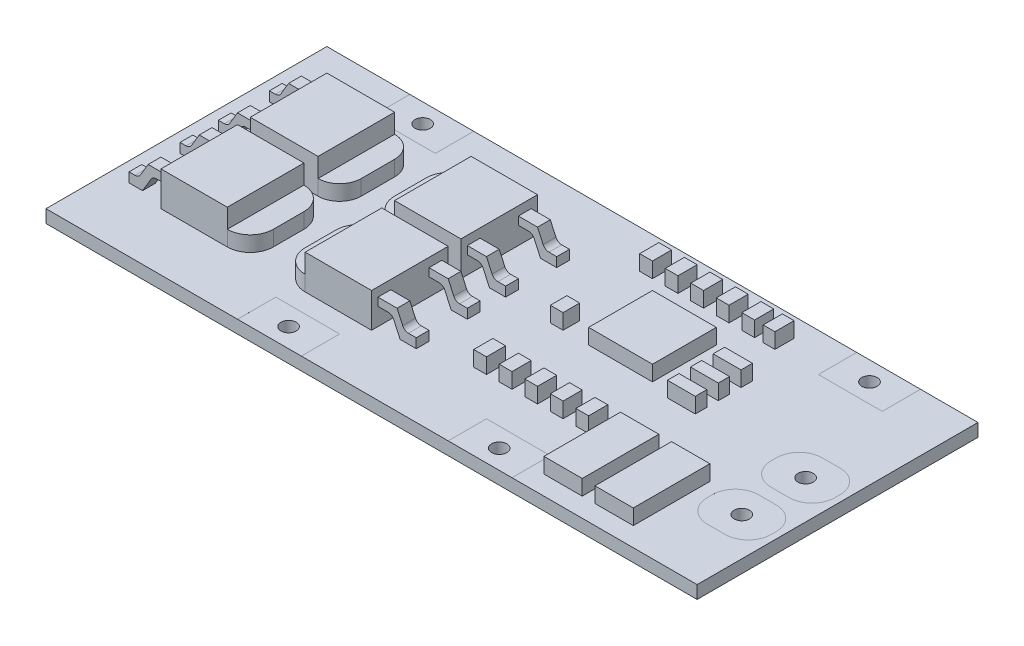
SolidWorks part; units mm, degrees
ref_plane "Front Plane" through (0, 0, 0) normal (0, 0, 1) x (1, 0, 0)
ref_plane "Top Plane" through (0, 0, 0) normal (0, 1, 0) x (1, 0, 0)
ref_plane "Right Plane" through (0, 0, 0) normal (1, 0, 0) x (0, 0, -1)
sketch "Sketch1" plane through (0, 0, 0) normal (0, 1, 0) x (1, 0, 0)
  line L1 (-25.5, 11) -> (25.5, 11)
  line L2 (-25.5, 11) -> (-25.5, -11)
  line L3 (-25.5, -11) -> (25.5, -11)
  line L4 (25.5, 11) -> (25.5, -11)
  circle A0 centre (22.5, 0.5) radius 0.6
  circle A1 centre (22.5, -4.5) radius 0.6
  circle A2 centre (18.5, 9.5) radius 0.6
  circle A3 centre (-16.5, 9.5) radius 0.6
  circle A4 centre (8.5, -9.5) radius 0.6
  circle A5 centre (-8, -9.5) radius 0.6
  point P4 (0, 11)
  point P6 (-25.5, 0)
  point P11 (25.5, 0)
  dimension "D6" = 1.2
  dimension "D7" = 1.2
  dimension "D10" = 1.2
  dimension "D13" = 1.2
  dimension "D16" = 1.2
  dimension "D19" = 1.2
  dimension "D1" = 22
  dimension "D2" = 51
  dimension "D3" = 0
  dimension "D4" = 0
  dimension "D5" = 5
  dimension "D8" = 11.5
  dimension "D9" = 3
  dimension "D11" = 7
  dimension "D12" = 1.5
  dimension "D14" = 35
  dimension "D15" = 1.5
  dimension "D17" = 17
  dimension "D18" = 1.5
  dimension "D20" = 16.5
  dimension "D21" = 1.5
  dimension "D22" = 3
extrude "Boss-Extrude1" add sketch "Sketch1" along normal blind 1 and the other way blind 0.01
sketch "Sketch2" plane through (0, 1, 0) normal (0, 1, 0) x (1, 0, 0)
  line L0 (25.5, 11) -> (-25.5, 11) construction
  line L1 (-19, 11) -> (-14, 11)
  line L2 (-19, 11) -> (-19, 8)
  line L3 (-19, 8) -> (-14, 8)
  line L4 (-14, 11) -> (-14, 8)
  line L5 (16, 11) -> (21, 11)
  line L6 (16, 11) -> (16, 8)
  line L7 (16, 8) -> (21, 8)
  line L8 (21, 11) -> (21, 8)
  line L9 (-25.5, -11) -> (25.5, -11) construction
  line L10 (-10.5, -8) -> (-5.5, -8)
  line L11 (-10.5, -8) -> (-10.5, -11)
  line L12 (-10.5, -11) -> (-5.5, -11)
  line L13 (-5.5, -8) -> (-5.5, -11)
  line L15 (6, -8) -> (11, -8)
  line L16 (6, -8) -> (6, -11)
  line L17 (6, -11) -> (11, -11)
  line L18 (11, -8) -> (11, -11)
  line L19 (21.8, 2.5) -> (23.2, 2.5)
  line L20 (20, 0.7) -> (20, 0.3)
  line L21 (21.8, -1.5) -> (23.2, -1.5)
  line L22 (25, 0.7) -> (25, 0.3)
  line L23 (21.8, -2.5) -> (23.2, -2.5)
  line L24 (20, -4.3) -> (20, -4.7)
  line L25 (21.8, -6.5) -> (23.2, -6.5)
  line L26 (25, -4.3) -> (25, -4.7)
  circle A0 centre (-16.5, 9.5) radius 0.6 construction
  circle A1 centre (18.5, 9.5) radius 0.6 construction
  circle A2 centre (-8, -9.5) radius 0.6 construction
  circle A3 centre (8.5, -9.5) radius 0.6 construction
  circle A4 centre (22.5, -4.5) radius 0.6 construction
  circle A5 centre (22.5, 0.5) radius 0.6 construction
  arc A6 (20, 0.3) -> (21.8, -1.5) centre (21.8, 0.3) ccw
  arc A7 (23.2, -1.5) -> (25, 0.3) centre (23.2, 0.3) ccw
  arc A8 (25, 0.7) -> (23.2, 2.5) centre (23.2, 0.7) ccw
  arc A9 (21.8, 2.5) -> (20, 0.7) centre (21.8, 0.7) ccw
  arc A10 (21.8, -2.5) -> (20, -4.3) centre (21.8, -4.3) ccw
  arc A11 (25, -4.3) -> (23.2, -2.5) centre (23.2, -4.3) ccw
  arc A12 (23.2, -6.5) -> (25, -4.7) centre (23.2, -4.7) ccw
  arc A13 (20, -4.7) -> (21.8, -6.5) centre (21.8, -4.7) ccw
  point P20 (-14, 9.5)
  point P41 (22.5, 2.5)
  dimension "D22" = 1.8
  dimension "D23" = 1.8
  dimension "D24" = 1.8
  dimension "D25" = 1.8
  dimension "D26" = 1.8
  dimension "D1" = 3
  dimension "D2" = 0
  dimension "D3" = 2.5
  dimension "D4" = 2.5
  dimension "D5" = 2.5
  dimension "D6" = 2.5
  dimension "D7" = 3
  dimension "D8" = 3
  dimension "D9" = 2.5
  dimension "D10" = 2.5
  dimension "D11" = 3
  dimension "D12" = 2.5
  dimension "D13" = 2.5
  dimension "D14" = 2.5
  dimension "D15" = 2.5
  dimension "D16" = 2
  dimension "D17" = 2
  dimension "D18" = 2
  dimension "D19" = 2
  dimension "D20" = 2.5
  dimension "D21" = 2.5
extrude "Cut-Extrude1" cut sketch "Sketch2" against normal blind 0.0001
sketch "Sketch3" plane through (0, -0.01, 0) normal (0, -1, 0) x (1, 0, 0)
  line L0 (25.5, -11) -> (-25.5, -11) construction
  line L1 (21, -11) -> (16, -11)
  line L2 (21, -11) -> (21, -8)
  line L3 (21, -8) -> (16, -8)
  line L4 (16, -11) -> (16, -8)
  line L5 (-14, -11) -> (-19, -11)
  line L6 (-14, -11) -> (-14, -8)
  line L7 (-14, -8) -> (-19, -8)
  line L8 (-19, -11) -> (-19, -8)
  line L9 (-25.5, 11) -> (25.5, 11) construction
  line L10 (-5.5, 11) -> (-10.5, 11)
  line L11 (-5.5, 11) -> (-5.5, 8)
  line L12 (-5.5, 8) -> (-10.5, 8)
  line L13 (-10.5, 11) -> (-10.5, 8)
  line L15 (11, 11) -> (6, 11)
  line L16 (11, 11) -> (11, 8)
  line L17 (11, 8) -> (6, 8)
  line L18 (6, 11) -> (6, 8)
  line L19 (23.2, 2.5) -> (21.8, 2.5)
  line L20 (25, 4.3) -> (25, 4.7)
  line L21 (23.2, 6.5) -> (21.8, 6.5)
  line L22 (20, 4.3) -> (20, 4.7)
  line L23 (23.2, -2.5) -> (21.8, -2.5)
  line L24 (25, -0.7) -> (25, -0.3)
  line L25 (23.2, 1.5) -> (21.8, 1.5)
  line L26 (20, -0.7) -> (20, -0.3)
  circle A0 centre (18.5, -9.5) radius 0.6 construction
  circle A1 centre (-16.5, -9.5) radius 0.6 construction
  circle A2 centre (-8, 9.5) radius 0.6 construction
  circle A3 centre (8.5, 9.5) radius 0.6 construction
  circle A4 centre (22.5, 4.5) radius 0.6 construction
  circle A5 centre (22.5, -0.5) radius 0.6 construction
  arc A6 (20, 4.3) -> (21.8, 2.5) centre (21.8, 4.3) ccw
  arc A7 (20, 4.7) -> (21.8, 6.5) centre (21.8, 4.7) cw
  arc A8 (23.2, 6.5) -> (25, 4.7) centre (23.2, 4.7) cw
  arc A9 (25, 4.3) -> (23.2, 2.5) centre (23.2, 4.3) cw
  arc A10 (25, -0.3) -> (23.2, 1.5) centre (23.2, -0.3) ccw
  arc A11 (21.8, 1.5) -> (20, -0.3) centre (21.8, -0.3) ccw
  arc A12 (20, -0.7) -> (21.8, -2.5) centre (21.8, -0.7) ccw
  arc A13 (23.2, -2.5) -> (25, -0.7) centre (23.2, -0.7) ccw
  dimension "D21" = 1.8
  dimension "D1" = 3
  dimension "D2" = 2.5
  dimension "D3" = 2.5
  dimension "D4" = 2.5
  dimension "D5" = 2.5
  dimension "D6" = 3
  dimension "D7" = 3
  dimension "D8" = 2.5
  dimension "D9" = 2.5
  dimension "D10" = 3
  dimension "D11" = 2.5
  dimension "D12" = 2.5
  dimension "D13" = 2
  dimension "D14" = 2
  dimension "D15" = 2.5
  dimension "D16" = 2.5
  dimension "D17" = 2
  dimension "D18" = 2
  dimension "D19" = 2.5
  dimension "D20" = 2.5
extrude "Cut-Extrude2" cut sketch "Sketch3" against normal blind 0.0001
sketch "Sketch4" plane through (0, -0.01, 0) normal (0, -1, 0) x (1, 0, 0)
  text T0 "XH-3S-D01" font "Century Gothic" height 2.5
extrude "Boss-Extrude2" add sketch "Sketch4" against normal blind 0.0001
sketch "Sketch5" plane through (0, 1, 0) normal (0, 1, 0) x (1, 0, 0)
  line L0 (25.5, -11) -> (25.5, 11) construction
  line L1 (19, -9.5) -> (16, -9.5)
  line L2 (19, -9.5) -> (19, -3.5)
  line L3 (19, -3.5) -> (16, -3.5)
  line L4 (16, -9.5) -> (16, -3.5)
  line L5 (15, -9.5) -> (12, -9.5)
  line L6 (15, -9.5) -> (15, -3.5)
  line L7 (15, -3.5) -> (12, -3.5)
  line L8 (12, -9.5) -> (12, -3.5)
  line L9 (11, -11) -> (25.5, -11) construction
  line L10 (16, 11) -> (-14, 11) construction
  line L11 (10, 1) -> (5, 1)
  line L12 (10, 1) -> (10, 6)
  line L13 (10, 6) -> (5, 6)
  line L14 (5, 1) -> (5, 6)
  line L15 (-25.5, 11) -> (-25.5, -11) construction
  line L16 (-4.5, -6.5) -> (-9.7, -6.5)
  line L17 (-4.5, -6.5) -> (-4.5, -0.5)
  line L18 (-4.5, -0.5) -> (-9.7, -0.5)
  line L19 (-11.5, -4.7) -> (-11.5, -2.3)
  line L20 (-4.5, 0.5) -> (-9.7, 0.5)
  line L21 (-4.5, 0.5) -> (-4.5, 6.5)
  line L22 (-4.5, 6.5) -> (-9.8079, 6.5)
  line L23 (-11.5, 2.3) -> (-11.5, 4.8079)
  line L24 (-15.8, -6.5) -> (-21, -6.5)
  line L25 (-14, -4.7) -> (-14, -2.3)
  line L26 (-15.8, -0.5) -> (-21, -0.5)
  line L27 (-21, -6.5) -> (-21, -0.5)
  line L28 (-15.6921, 0.5) -> (-21, 0.5)
  line L29 (-14, 2.1921) -> (-14, 4.8079)
  line L30 (-15.6921, 6.5) -> (-21, 6.5)
  line L31 (-21, 0.5) -> (-21, 6.5)
  line L32 (-25.5, -11) -> (-10.5, -11) construction
  line L33 (-19, 11) -> (-25.5, 11) construction
  line L34 (-5.5, -11) -> (6, -11) construction
  line L35 (6, -11) -> (11, -11) construction
  line L36 (11, -5) -> (10, -5)
  line L37 (11, -5) -> (11, -3.5)
  line L38 (11, -3.5) -> (10, -3.5)
  line L39 (10, -5) -> (10, -3.5)
  line L40 (9, -5) -> (8, -5)
  line L41 (8, -5) -> (8, -3.5)
  line L42 (9, -5) -> (9, -3.5)
  line L43 (9, -3.5) -> (8, -3.5)
  line L44 (7, -5) -> (6, -5)
  line L45 (6, -5) -> (6, -3.5)
  line L46 (7, -5) -> (7, -3.5)
  line L47 (7, -3.5) -> (6, -3.5)
  line L48 (5, -5) -> (4, -5)
  line L49 (4, -5) -> (4, -3.5)
  line L50 (5, -5) -> (5, -3.5)
  line L51 (5, -3.5) -> (4, -3.5)
  line L52 (3, -5) -> (2, -5)
  line L53 (2, -5) -> (2, -3.5)
  line L54 (3, -5) -> (3, -3.5)
  line L55 (3, -3.5) -> (2, -3.5)
  line L56 (9, 8) -> (8, 8)
  line L57 (8, 8) -> (8, 9.5)
  line L58 (9, 8) -> (9, 9.5)
  line L59 (9, 9.5) -> (8, 9.5)
  line L60 (7, 8) -> (6, 8)
  line L61 (6, 8) -> (6, 9.5)
  line L62 (7, 8) -> (7, 9.5)
  line L63 (7, 9.5) -> (6, 9.5)
  line L64 (5, 8) -> (4, 8)
  line L65 (4, 8) -> (4, 9.5)
  line L66 (5, 8) -> (5, 9.5)
  line L67 (5, 9.5) -> (4, 9.5)
  line L68 (3, 8) -> (2, 8)
  line L69 (2, 8) -> (2, 9.5)
  line L70 (3, 8) -> (3, 9.5)
  line L71 (3, 9.5) -> (2, 9.5)
  line L72 (11, 8) -> (10, 8)
  line L73 (10, 8) -> (10, 9.5)
  line L74 (11, 8) -> (11, 9.5)
  line L75 (11, 9.5) -> (10, 9.5)
  line L77 (11.6733, 8) -> (12.5928, 8)
  line L78 (11.6733, 8) -> (11.6733, 9.5)
  line L79 (11.6733, 9.5) -> (12.5928, 9.5)
  line L80 (12.5928, 8) -> (12.5928, 9.5)
  line L81 (3, 1) -> (2, 1)
  line L82 (3, 1) -> (3, 2.3)
  line L83 (3, 2.3) -> (2, 2.3)
  line L84 (2, 1) -> (2, 2.3)
  line L85 (11.6733, 0.5) -> (13.8567, 0.5)
  line L86 (11.6733, 0.5) -> (11.6733, 1.4052)
  line L87 (11.6733, 1.4052) -> (13.8567, 1.4052)
  line L88 (13.8567, 0.5) -> (13.8567, 1.4052)
  line L89 (11.6733, 2.3) -> (13.8567, 2.3)
  line L90 (11.6733, 2.3) -> (11.6733, 3.185)
  line L91 (11.6733, 3.185) -> (13.8567, 3.185)
  line L92 (13.8567, 2.3) -> (13.8567, 3.185)
  line L93 (11.6733, 4.0827) -> (13.8567, 4.0827)
  line L94 (11.6733, 4.0827) -> (11.6733, 4.9804)
  line L95 (11.6733, 4.9804) -> (13.8567, 4.9804)
  line L96 (13.8567, 4.0827) -> (13.8567, 4.9804)
  arc A0 (-11.5, -4.7) -> (-9.7, -6.5) centre (-9.7, -4.7) ccw
  arc A1 (-11.5, -2.3) -> (-9.7, -0.5) centre (-9.7, -2.3) cw
  arc A2 (-15.8, -6.5) -> (-14, -4.7) centre (-15.8, -4.7) ccw
  arc A3 (-15.8, -0.5) -> (-14, -2.3) centre (-15.8, -2.3) cw
  arc A4 (-11.5, 2.3) -> (-9.7, 0.5) centre (-9.7, 2.3) ccw
  arc A5 (-15.6921, 0.5) -> (-14, 2.1921) centre (-15.6921, 2.1921) ccw
  arc A6 (-15.6921, 6.5) -> (-14, 4.8079) centre (-15.6921, 4.8079) cw
  arc A7 (-11.5, 4.8079) -> (-9.8079, 6.5) centre (-9.8079, 4.8079) cw
  point P10 (17.5, -9.5)
  point P45 (-11.5, -6.5)
  point P50 (-14, -6.5)
  point P55 (-11.5, 0.5)
  point P58 (-14, 0.5)
  dimension "D29" = 1.8
  dimension "D30" = 1.8
  dimension "D31" = 1.8
  dimension "D32" = 1.8
  dimension "D33" = 1.8
  dimension "D34" = 1.6921
  dimension "D1" = 3
  dimension "D2" = 6
  dimension "D3" = 3
  dimension "D4" = 9.5
  dimension "D5" = 13.5
  dimension "D6" = 1.5
  dimension "D7" = 1.5
  dimension "D8" = 6
  dimension "D9" = 5
  dimension "D10" = 5
  dimension "D11" = 5
  dimension "D12" = 15.5
  dimension "D13" = 7
  dimension "D14" = 6
  dimension "D15" = 6
  dimension "D16" = 7
  dimension "D17" = 7
  dimension "D18" = 6
  dimension "D19" = 6
  dimension "D20" = 7
  dimension "D21" = 4.5
  dimension "D22" = 4.5
  dimension "D23" = 14
  dimension "D24" = 14
  dimension "D25" = 4.5
  dimension "D26" = 4.5
  dimension "D27" = 4.5
  dimension "D28" = 4.5
  dimension "D35" = 1
  dimension "D36" = 1.5
  dimension "D37" = 6
  dimension "D38" = 14.5
  dimension "D39" = 5
  dimension "D40" = 2
extrude "Boss-Extrude3" add sketch "Sketch5" along normal blind 1.2
sketch "Sketch6" plane through (0, 2.2, 0) normal (0, 1, 0) x (1, 0, 0)
  line L0 (-4.5, 6.5) -> (-9.8079, 6.5) construction
  line L1 (-4.5, -6.5) -> (-9.7, -6.5)
  line L2 (-4.5, -6.5) -> (-4.5, -0.5)
  line L3 (-4.5, -0.5) -> (-9.7, -0.5)
  line L4 (-9.7, -6.5) -> (-9.7, -0.5)
  line L5 (-4.5, 0.5) -> (-9.7, 0.5)
  line L6 (-4.5, 0.5) -> (-4.5, 6.5)
  line L7 (-4.5, 6.5) -> (-9.7, 6.5)
  line L8 (-9.7, 0.5) -> (-9.7, 6.5)
  line L10 (-21, 6.5) -> (-15.6921, 6.5)
  line L11 (-21, 6.5) -> (-21, 0.5)
  line L12 (-21, 0.5) -> (-15.6921, 0.5)
  line L13 (-15.6921, 6.5) -> (-15.6921, 0.5)
  line L14 (-21, -0.5) -> (-15.8, -0.5)
  line L15 (-21, -0.5) -> (-21, -6.5)
  line L16 (-21, -6.5) -> (-15.8, -6.5)
  line L17 (-15.8, -0.5) -> (-15.8, -6.5)
  arc A0 (-15.6921, 0.5) -> (-14, 2.1921) centre (-15.6921, 2.1921) ccw construction
  arc A1 (-15.6921, 0.5) -> (-14, 2.1921) centre (-15.6921, 2.1921) ccw construction
  arc A2 (-15.8, -6.5) -> (-14, -4.7) centre (-15.8, -4.7) ccw construction
  arc A3 (-15.8, -6.5) -> (-14, -4.7) centre (-15.8, -4.7) ccw construction
extrude "Boss-Extrude4" add sketch "Sketch6" along normal blind 1.5
sketch "Sketch7" plane through (0, 1, 0) normal (0, 1, 0) x (1, 0, 0)
  line L0 (-4.5, -6.5) -> (-4.5, -0.5) construction
  line L1 (-4.5, -6) -> (-1.5, -6)
  line L2 (-4.5, -6) -> (-4.5, -5)
  line L3 (-4.5, -5) -> (-1.5, -5)
  line L4 (-1.5, -6) -> (-1.5, -5)
  line L5 (-9.7, -6.5) -> (-4.5, -6.5) construction
  line L6 (-4.5, -0.5) -> (-9.7, -0.5) construction
  line L7 (-4.5, -1) -> (-1.5, -1)
  line L8 (-4.5, -1) -> (-4.5, -2)
  line L9 (-4.5, -2) -> (-1.5, -2)
  line L10 (-1.5, -1) -> (-1.5, -2)
  line L11 (-4.5, 0.5) -> (-4.5, 6.5) construction
  line L12 (-4.5, 1) -> (-1.5, 1)
  line L13 (-4.5, 1) -> (-4.5, 2)
  line L14 (-4.5, 2) -> (-1.5, 2)
  line L15 (-1.5, 1) -> (-1.5, 2)
  line L16 (-4.5, 0.5) -> (-4.5, 6.5) construction
  line L17 (-4.5, 6) -> (-1.5, 6)
  line L18 (-4.5, 6) -> (-4.5, 5)
  line L19 (-4.5, 5) -> (-1.5, 5)
  line L20 (-1.5, 6) -> (-1.5, 5)
  line L21 (-9.7, 0.5) -> (-4.5, 0.5) construction
  line L22 (-4.5, 6.5) -> (-9.7, 6.5) construction
  line L23 (-21, -0.5) -> (-21, -6.5) construction
  line L24 (-21, -6) -> (-24, -6)
  line L25 (-21, -6) -> (-21, -5)
  line L26 (-21, -5) -> (-24, -5)
  line L27 (-24, -6) -> (-24, -5)
  line L28 (-21, -0.5) -> (-21, -6.5) construction
  line L29 (-21, -2) -> (-24, -2)
  line L30 (-21, -2) -> (-21, -1)
  line L31 (-21, -1) -> (-24, -1)
  line L32 (-24, -2) -> (-24, -1)
  line L33 (-21, 6.5) -> (-21, 0.5) construction
  line L34 (-21, 1) -> (-24, 1)
  line L35 (-21, 1) -> (-21, 2)
  line L36 (-21, 2) -> (-24, 2)
  line L37 (-24, 1) -> (-24, 2)
  line L38 (-21, 6.5) -> (-21, 0.5) construction
  line L39 (-21, 5) -> (-24, 5)
  line L40 (-21, 5) -> (-21, 6)
  line L41 (-21, 6) -> (-24, 6)
  line L42 (-24, 5) -> (-24, 6)
  dimension "D1" = 3
  dimension "D2" = 1
  dimension "D3" = 0.5
  dimension "D4" = 1
  dimension "D5" = 0.5
  dimension "D6" = 1
  dimension "D7" = 0.5
  dimension "D8" = 0.5
  dimension "D9" = 1
  dimension "D10" = 3
  dimension "D11" = 3
  dimension "D12" = 3
  dimension "D13" = 3
extrude "Boss-Extrude5" add sketch "Sketch7" along normal blind 2
sketch "Sketch8" plane through (0, 0, -6) normal (0, 0, -1) x (-1, 0, 0)
  line L0 (3, 3) -> (2.5627, 2.0398)
  line L1 (1.5, 3) -> (4.5, 3) construction
  line L2 (2.1077, 1.747) -> (1.5, 1.747)
  line L3 (1.5, 3) -> (1.5, 1) construction
  line L4 (1.5, 1.747) -> (1.5, 3)
  line L5 (1.5, 3) -> (3, 3)
  line L6 (22.5, 3) -> (23.1022, 1.9908)
  line L7 (21, 3) -> (24, 3) construction
  line L8 (23.5316, 1.747) -> (24, 1.747)
  line L9 (24, 3) -> (24, 1) construction
  line L10 (24, 1.747) -> (24, 3)
  line L11 (24, 3) -> (22.5, 3)
  line L12 (4.5, 2.3735) -> (3.7115, 2.3735)
  line L13 (4.5, 3) -> (4.5, 1) construction
  line L14 (3.2564, 2.0807) -> (2.7643, 1)
  line L15 (-16, 1) -> (14, 1) construction
  line L16 (2.7643, 1) -> (4.5, 1)
  line L17 (4.5, 1) -> (4.5, 2.3735)
  line L18 (21, 2.35) -> (21.8492, 2.35)
  line L19 (21, 3.7) -> (21, 1) construction
  line L20 (22.2785, 2.1062) -> (22.9386, 1)
  line L21 (21, 1) -> (24, 1) construction
  line L22 (22.9386, 1) -> (21, 1)
  line L23 (21, 1) -> (21, 2.35)
  arc A0 (23.5316, 1.747) -> (23.1022, 1.9908) centre (23.5316, 2.247) cw
  arc A1 (22.2785, 2.1062) -> (21.8492, 2.35) centre (21.8492, 1.85) ccw
  arc A2 (2.5627, 2.0398) -> (2.1077, 1.747) centre (2.1077, 2.247) cw
  arc A3 (3.7115, 2.3735) -> (3.2564, 2.0807) centre (3.7115, 1.8735) ccw
  dimension "D1" = 0.5
extrude "Cut-Extrude5" cut sketch "Sketch8" against normal through all
